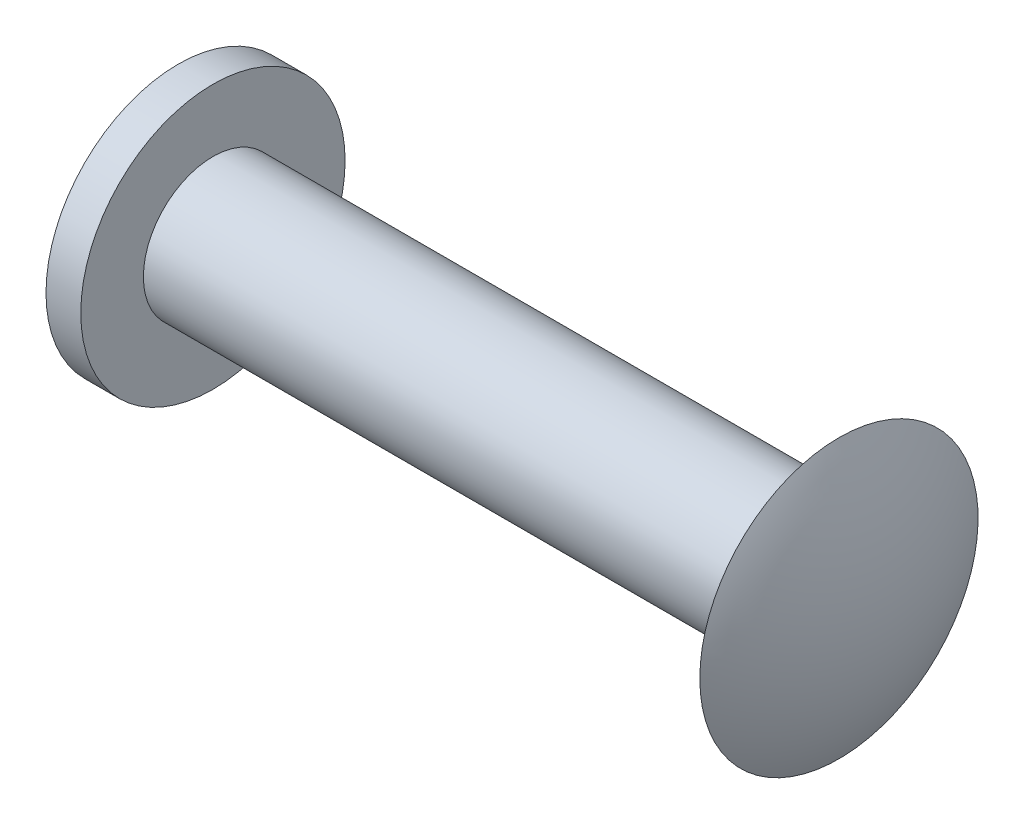
SolidWorks part; units mm, degrees
material "3.1325 (EN-AW 2017A)"
ref_plane "Płaszczyzna przednia" through (0, 0, 0) normal (0, 0, 1) x (1, 0, 0)
ref_plane "Płaszczyzna górna" through (0, 0, 0) normal (0, 1, 0) x (1, 0, 0)
ref_plane "Płaszczyzna prawa" through (0, 0, 0) normal (1, 0, 0) x (0, 0, -1)
sketch "Szkic1" plane through (0, 0, 0) normal (0, 0, 1) x (1, 0, 0)
  line L0 (0, 0) -> (9.5, 0)
  line L1 (0, 0) -> (0, 1.9)
  line L2 (0, 1.9) -> (0.5, 1.9)
  line L3 (0.5, 1.9) -> (0.5, 1)
  line L4 (0.5, 1) -> (9.5, 1)
  line L5 (9.5, 1) -> (9.5, 2)
  line L6 (9.5, 0) -> (10, 0) construction
  line L7 (10, 0) -> (10, -1.7727) construction
  line L8 (9.5, 0) -> (10, 0)
  arc A0 (9.5, 2) -> (10, 0) centre (5.75, 0) cw
  dimension "D1" = 2
  dimension "D2" = 9
  dimension "D3" = 0.5
  dimension "D4" = 10
  dimension "D5" = 4
  dimension "D6" = 0.5
  dimension "D7" = 3.8
revolve "Obrót1" add sketch "Szkic1" angle 360 about L8
